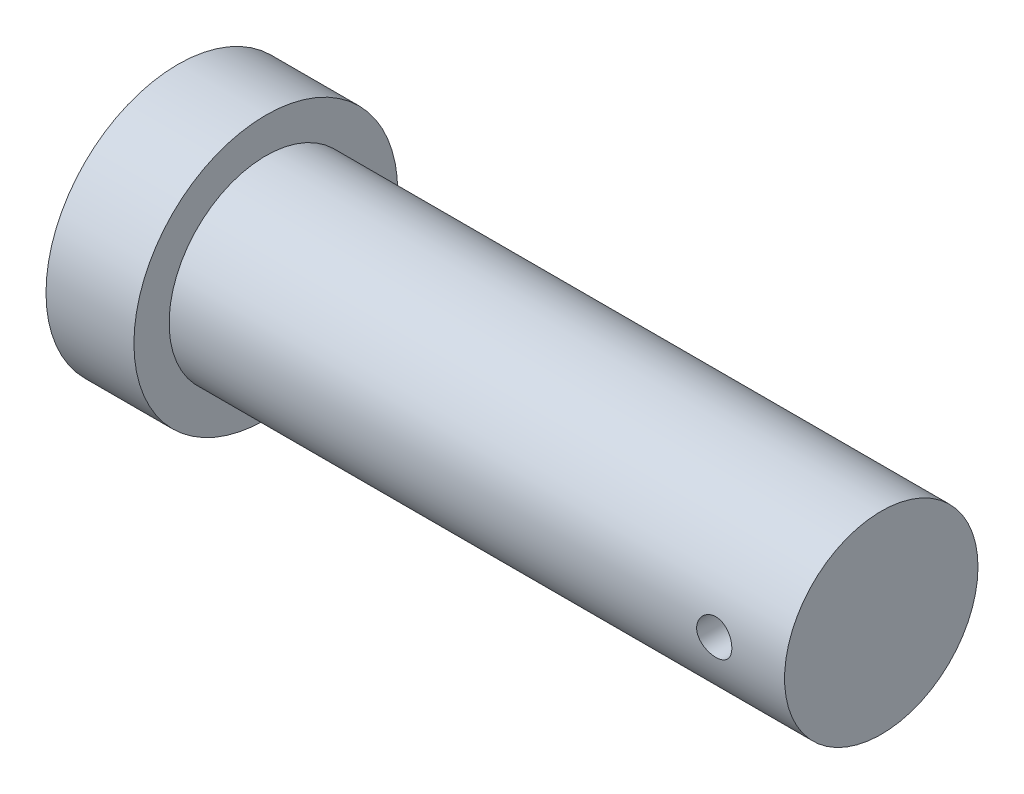
SolidWorks part; units mm, degrees
material "6063-T6"
ref_plane "Front Plane" through (0, 0, 0) normal (0, 0, 1) x (1, 0, 0)
ref_plane "Top Plane" through (0, 0, 0) normal (0, 1, 0) x (1, 0, 0)
ref_plane "Right Plane" through (0, 0, 0) normal (1, 0, 0) x (0, 0, -1)
sketch "Sketch1" plane through (0, 0, 0) normal (1, 0, 0) x (0, 0, -1)
  circle A0 centre (0, 0) radius 5.5
  dimension "D1" = 11
extrude "Boss-Extrude1" add sketch "Sketch1" against normal blind 35
sketch "Sketch2" plane through (-35, 0, 0) normal (-1, 0, 0) x (0, 0, 1)
  circle A0 centre (0, 0) radius 7.5
  dimension "D1" = 15
extrude "Boss-Extrude2" add sketch "Sketch2" along normal blind 5
sketch "Sketch3" plane through (0, 0, 0) normal (0, 0, 1) x (1, 0, 0)
  line L0 (0, -5.5) -> (0, 5.5) construction
  circle A0 centre (-4, 0) radius 1
  dimension "D2" = 2
  dimension "D1" = 4
extrude "Cut-Extrude1" cut sketch "Sketch3" against normal through all both and the other way through all
